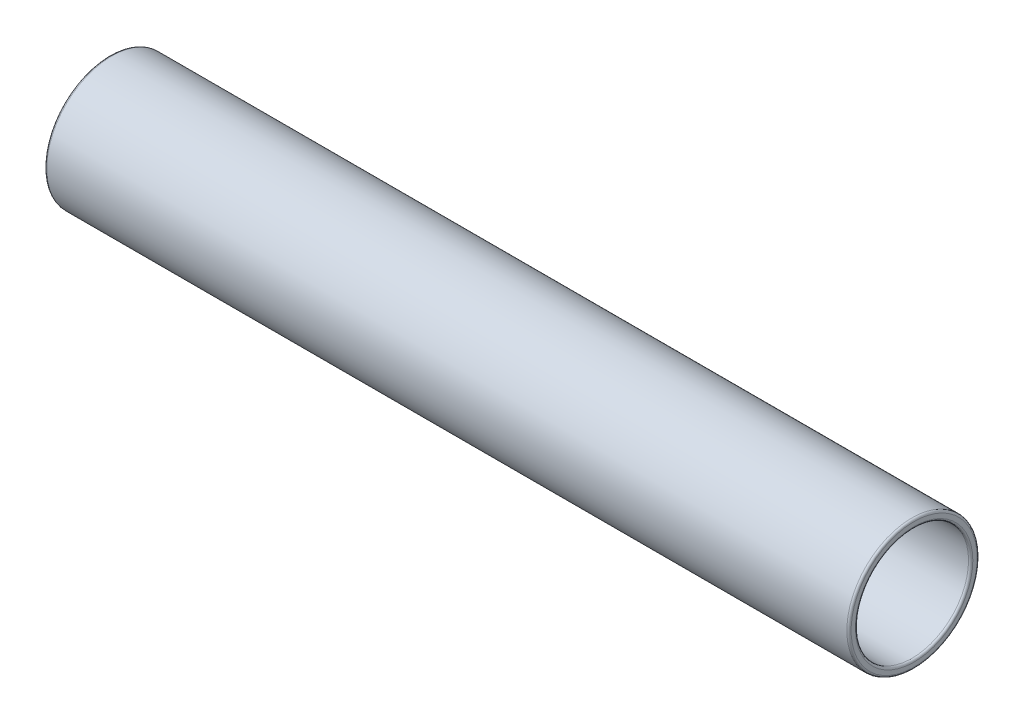
SolidWorks part; units mm, degrees
ref_plane "Front Plane" through (0, 0, 0) normal (0, 0, 1) x (1, 0, 0)
ref_plane "Top Plane" through (0, 0, 0) normal (0, 1, 0) x (1, 0, 0)
ref_plane "Right Plane" through (0, 0, 0) normal (1, 0, 0) x (0, 0, -1)
sketch "Sketch1" plane through (0, 0, 0) normal (1, 0, 0) x (0, 0, -1)
  circle A0 centre (0, 0) radius 60.75
  circle A1 centre (0, 0) radius 52.75
  dimension "D1" = 8
extrude "Boss-Extrude1" add sketch "Sketch1" along normal blind 750
fillet "Fillet1" radius 2 2 edges at (750, 0, -52.75) (750, 0, -60.75)
fillet "Fillet2" radius 2 2 edges at (0, 0, -52.75) (0, 0, -60.75)
